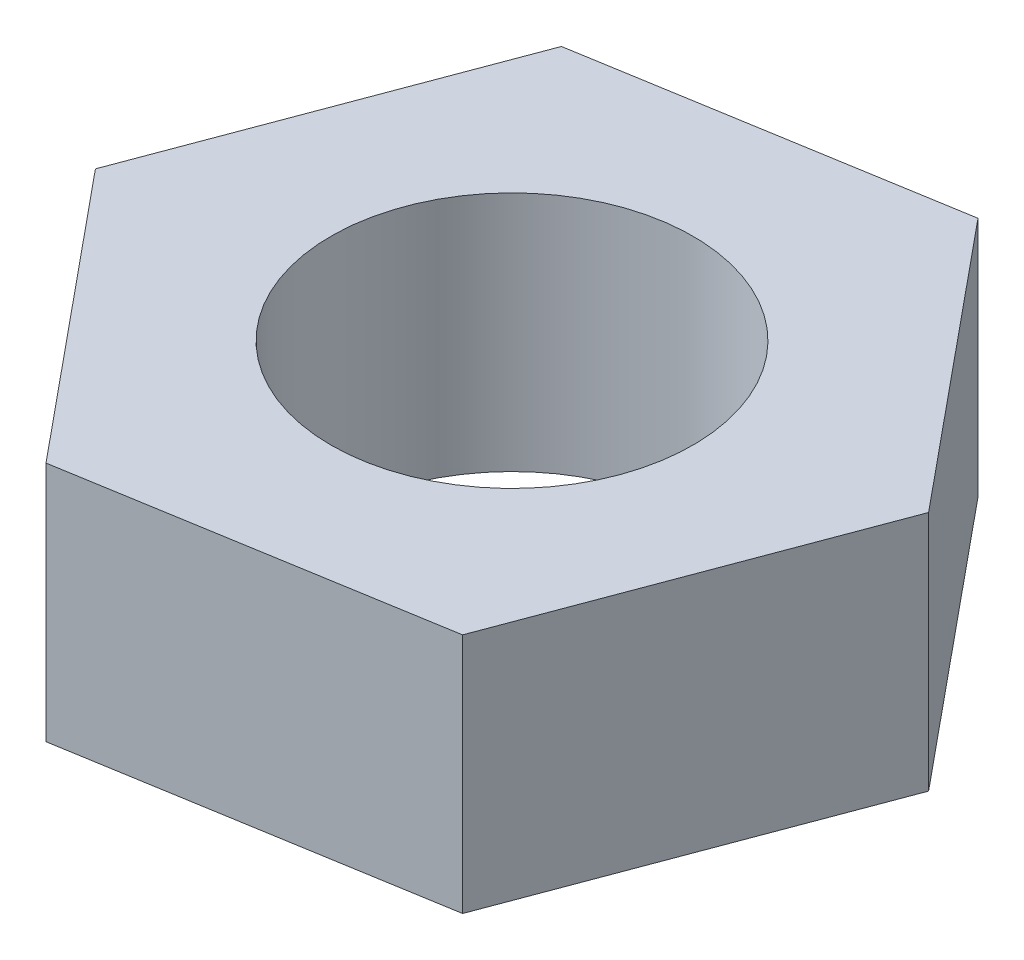
SolidWorks part; units mm, degrees
ref_plane "Front Plane" through (0, 0, 0) normal (0, 0, 1) x (1, 0, 0)
ref_plane "Top Plane" through (0, 0, 0) normal (0, 1, 0) x (1, 0, 0)
ref_plane "Right Plane" through (0, 0, 0) normal (1, 0, 0) x (0, 0, -1)
sketch "Sketch1" plane through (0, 0, 0) normal (0, 1, 0) x (1, 0, 0)
  line L1 (2.9592, 0.4932) -> (1.0525, 2.8093)
  line L2 (1.0525, 2.8093) -> (-1.9067, 2.3161)
  line L3 (-1.9067, 2.3161) -> (-2.9592, -0.4932)
  line L4 (-2.9592, -0.4932) -> (-1.0525, -2.8093)
  line L5 (-1.0525, -2.8093) -> (1.9067, -2.3161)
  line L6 (1.9067, -2.3161) -> (2.9592, 0.4932)
  circle A0 centre (0, 0) radius 1.5
  circle A1 centre (0, 0) radius 2.5981 construction
  dimension "D1" = 3
  dimension "D2" = 6
extrude "Boss-Extrude2" add sketch "Sketch1" along normal blind 2
equation "\"thread_dist\"= 3.5"
equation "\"thread_diameter\"= 3"
equation "\"D13@Sketch1\"=\"thread_diameter\""
equation "\"D14@Sketch1\"=\"thread_dist\""
equation "\"D11@Sketch1\"=\"thread_diameter\""
equation "\"D12@Sketch1\"=\"thread_dist\""
equation "\"D8@Sketch1\"=\"thread_diameter\""
equation "\"D10@Sketch1\"=\"thread_dist\""
equation "\"D1@Sketch1\"=\"thread_diameter\""
equation "\"thread_length\"=12"
equation "\"D1@Boss-Extrude1\"=\"thread_length\""
